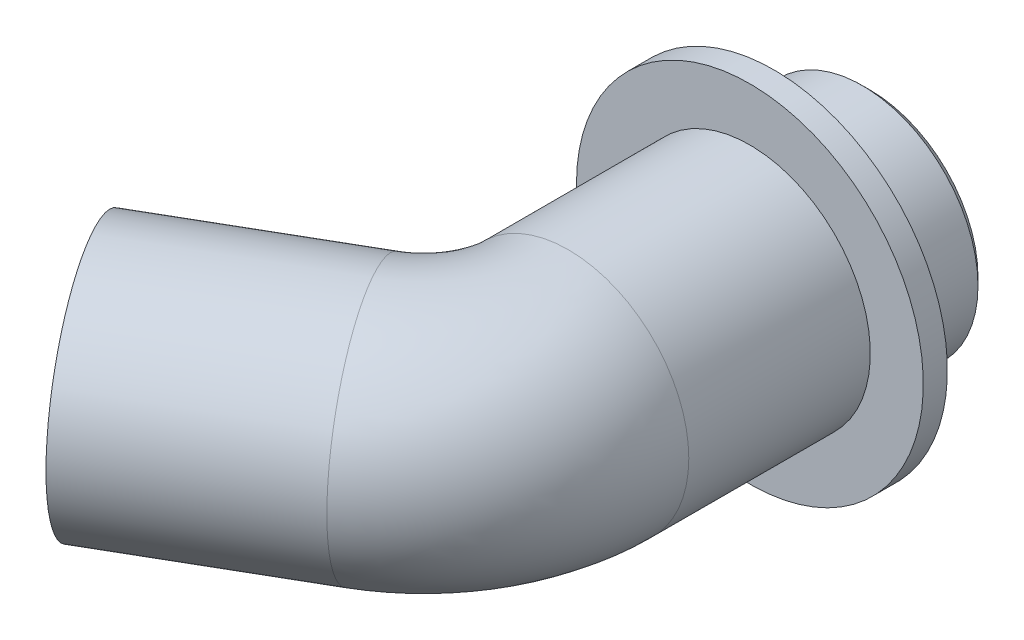
SolidWorks part; units mm, degrees
material "Бронза"
ref_plane "Спереди" through (0, 0, 0) normal (0, 0, 1) x (1, 0, 0)
ref_plane "Сверху" through (0, 0, 0) normal (0, 1, 0) x (1, 0, 0)
ref_plane "Справа" through (0, 0, 0) normal (1, 0, 0) x (0, 0, -1)
sketch "Эскиз1" plane through (0, 0, 0) normal (0, 0, 1) x (1, 0, 0)
  circle A0 centre (0, 0) radius 25
  circle A1 centre (0, 0) radius 15
  dimension "D1" = 50
  dimension "D2" = 30
sketch "Эскиз2" plane through (0, 0, 0) normal (0, 1, 0) x (1, 0, 0)
  line L0 (0, 0) -> (0, -62.6795)
  line L1 (-25, 0) -> (25, 0) construction
  line L2 (-15, -88.6603) -> (-51.9615, -110)
  line L3 (0, -80) -> (-40.494, -80) construction
  arc A0 (0, -62.6795) -> (-15, -88.6603) centre (-30, -62.6795) cw
  dimension "D4" = 30
  dimension "D1" = 80
  dimension "D2" = 30
  dimension "D3" = 60
sweep "По траектории1" add profiles "Эскиз1" path "Эскиз2"
sketch "Эскиз3" plane through (0, 0, 0) normal (0, 0, -1) x (-1, 0, 0)
  circle A0 centre (0, 0) radius 36
  circle A1 centre (0, 0) radius 25
  circle A2 centre (0, 0) radius 25 construction
  dimension "D1" = 72
extrude "Бобышка-Вытянуть2" add sketch "Эскиз3" against normal blind 5 from offset 20 offset against normal yes
sketch "Эскиз4" plane through (0, 0, 0) normal (0, 1, 0) x (1, 0, 0)
  line L0 (36, -20) -> (-36, -20) construction
  line L1 (22, -16) -> (32, -16)
  line L2 (22, -16) -> (22, -20)
  line L3 (22, -20) -> (32, -20)
  line L4 (32, -16) -> (32, -20)
  line L5 (0, 0) -> (0, -25) construction
  line L6 (25, 0) -> (-25, 0) construction
  line L7 (-25, -25) -> (25, -25) construction
  dimension "D1" = 44
  dimension "D2" = 10
  dimension "D3" = 4
revolve "Вырез-Повернуть1" cut sketch "Эскиз4" angle 360 about L5
sketch "Эскиз5" plane through (0, 0, 0) normal (0, 0, -1) x (-1, 0, 0)
  circle A0 centre (0, 0) radius 24
  circle A1 centre (0, 0) radius 25
  circle A2 centre (0, 0) radius 25
  dimension "D2" = 48
  dimension "D1" = 0
extrude "Вырез-Вытянуть1" cut sketch "Эскиз5" against normal up to next
cosmetic thread "Условное изображение резьбы1" parameters "D2"=44.704
chamfer "Фаска1" distance 1.648 angle 45 1 edges at (-24, 0, 0)
